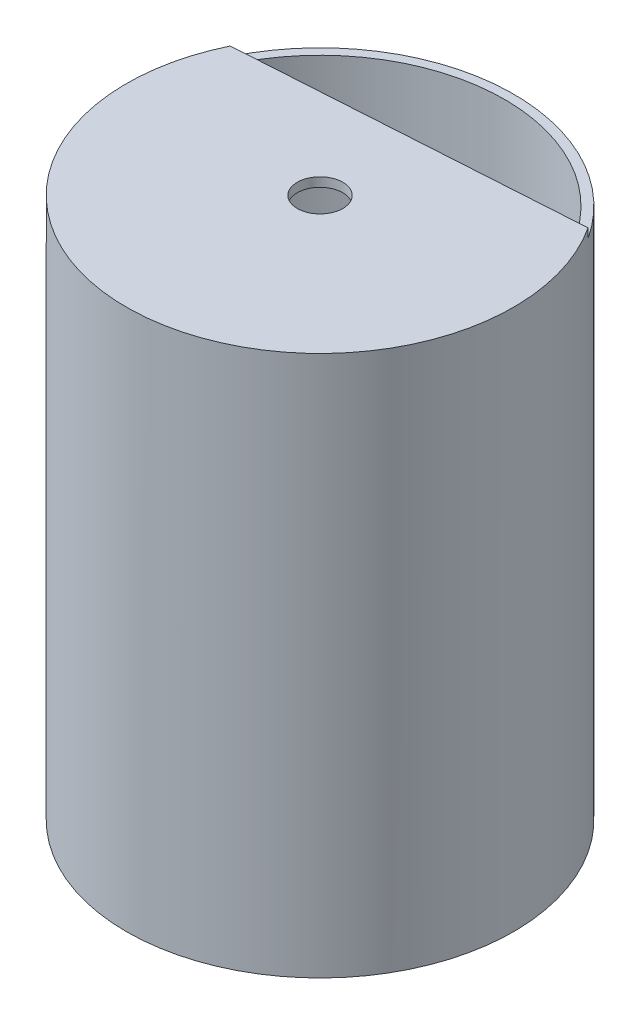
SolidWorks part; units mm, degrees
ref_plane "Front Plane" through (0, 0, 0) normal (0, 0, 1) x (1, 0, 0)
ref_plane "Top Plane" through (0, 0, 0) normal (0, 1, 0) x (1, 0, 0)
ref_plane "Right Plane" through (0, 0, 0) normal (1, 0, 0) x (0, 0, -1)
sketch "Sketch1" plane through (0, 0, 0) normal (0, 1, 0) x (1, 0, 0)
  circle A0 centre (0, 0) radius 10.795
  circle A1 centre (0, 0) radius 10.287
  dimension "D1" = 21.59
  dimension "D2" = 20.574
extrude "Boss-Extrude1" add sketch "Sketch1" along normal blind 29.6418 contours A0 | A1
sketch "Sketch2" plane through (0, 29.6418, 0) normal (0, 1, 0) x (1, 0, 0)
  line L0 (-9.714, 4.7085) -> (9.0391, 5.9015)
  circle A0 centre (0, 0) radius 10.795
  circle M2 centre (0, 0) radius 10.795
  circle M3 centre (0, 0) radius 10.287
extrude "Boss-Extrude3" add sketch "Sketch2" along normal blind 0.508 contours L0 M3 | L0 M2 M3
sketch "Sketch3" plane through (0, 30.1498, 0) normal (0, 1, 0) x (1, 0, 0)
  circle A0 centre (0, 0) radius 1.27
  dimension "D1" = 2.54
extrude "Cut-Extrude1" cut sketch "Sketch3" against normal through all
sketch "Sketch6" plane through (0, 0, 0) normal (0, -1, 0) x (1, 0, 0)
  line L0 (4.8217, 7.2084) -> (-3.8694, 7.7613) construction
  line L1 (6.2911, -8.216) -> (-7.2815, -7.3526) construction
  line L2 (8.2246, 6.992) -> (-7.2723, 7.9778)
  line L3 (6.9525, -8.258) -> (-7.9428, -7.3105)
  line L4 (6.2911, -8.216) -> (-7.2815, -7.3526)
  line L5 (4.8217, 7.2084) -> (-3.8694, 7.7613)
  circle A0 centre (0, 0) radius 10.795
  circle M3 centre (0, 0) radius 10.287
extrude "Boss-Extrude4" add sketch "Sketch6" against normal up to next contours L2 M3
sketch "Sketch8" plane through (0, 0, 0) normal (0, -1, 0) x (1, 0, 0)
  line L0 (-7.9428, -7.3105) -> (6.9525, -8.258)
  circle A0 centre (0, 0) radius 10.795
  arc M2 (7.5027, 7.0379) -> (-6.5504, 7.9319) centre (0, 0) cw
extrude "Boss-Extrude5" [suppressed] add sketch "Sketch8" against normal blind 19.558 contours L0 M2
